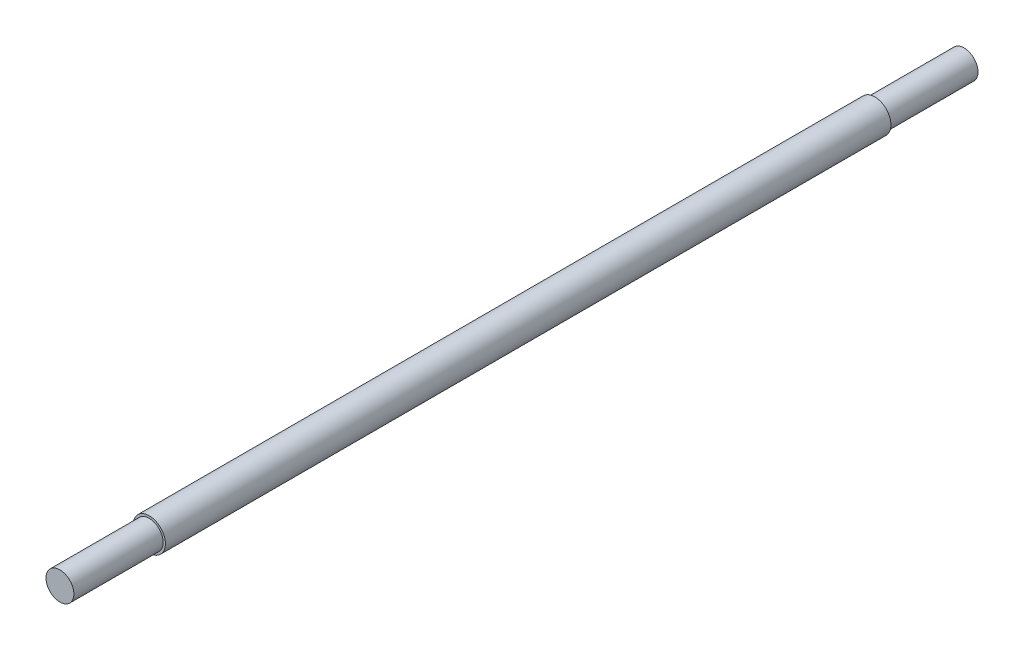
SolidWorks part; units mm, degrees
ref_plane "Front Plane" through (0, 0, 0) normal (0, 0, 1) x (1, 0, 0)
ref_plane "Top Plane" through (0, 0, 0) normal (0, 1, 0) x (1, 0, 0)
ref_plane "Right Plane" through (0, 0, 0) normal (1, 0, 0) x (0, 0, -1)
sketch "Sketch1" plane through (0, 0, 0) normal (0, 0, 1) x (1, 0, 0)
  circle A0 centre (0, 0) radius 14.5
  dimension "D1" = 29
extrude "Boss-Extrude1" add sketch "Sketch1" along normal mid plane 650
sketch "Sketch2" plane through (0, 0, 325) normal (0, 0, 1) x (1, 0, 0)
  circle A0 centre (0, 0) radius 12.5
  dimension "D1" = 25
extrude "Boss-Extrude2" add sketch "Sketch2" along normal blind 80 separate body
mirror "Mirror1" about plane through (0, 0, 0) normal (0, 0, 1) of bodies 102
